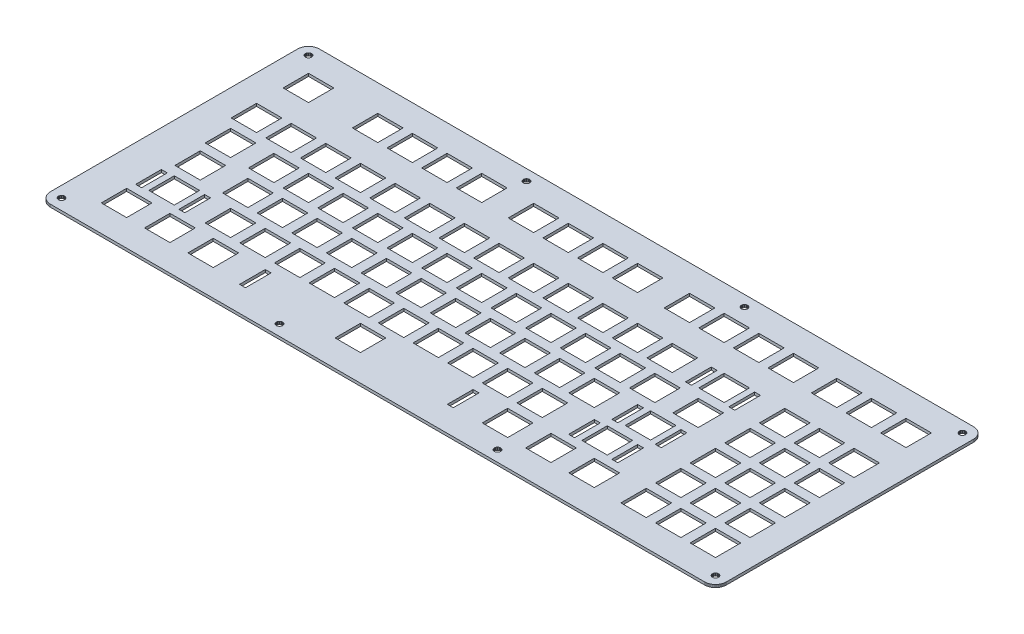
SolidWorks part; units mm, degrees
material "Copper"
ref_plane "Front Plane" through (0, 0, 0) normal (0, 0, 1) x (1, 0, 0)
ref_plane "Top Plane" through (0, 0, 0) normal (0, 1, 0) x (1, 0, 0)
ref_plane "Right Plane" through (0, 0, 0) normal (1, 0, 0) x (0, 0, -1)
sketch "Sketch2" plane through (0, 0, 0) normal (0, 1, 0) x (1, 0, 0)
  line L0 (365.806, 147.967) -> (366.279, 147.949)
  line L1 (366.279, 147.949) -> (366.748, 147.894)
  line L2 (366.748, 147.894) -> (367.21, 147.803)
  line L3 (367.21, 147.803) -> (367.661, 147.675)
  line L4 (367.661, 147.675) -> (368.106, 147.511)
  line L5 (368.106, 147.511) -> (368.533, 147.314)
  line L6 (368.533, 147.314) -> (368.942, 147.085)
  line L7 (368.942, 147.085) -> (369.334, 146.822)
  line L8 (369.334, 146.822) -> (369.704, 146.529)
  line L9 (369.704, 146.529) -> (370.05, 146.21)
  line L10 (370.05, 146.21) -> (370.371, 145.865)
  line L11 (370.371, 145.865) -> (370.664, 145.495)
  line L12 (370.664, 145.495) -> (370.925, 145.102)
  line L13 (370.925, 145.102) -> (371.154, 144.691)
  line L14 (371.154, 144.691) -> (371.352, 144.264)
  line L15 (371.352, 144.264) -> (371.514, 143.822)
  line L16 (371.514, 143.822) -> (371.641, 143.368)
  line L17 (371.641, 143.368) -> (371.733, 142.907)
  line L18 (371.733, 142.907) -> (371.789, 142.44)
  line L19 (371.789, 142.44) -> (371.807, 141.967)
  line L20 (371.807, 141.967) -> (371.807, 6.0909)
  line L21 (371.807, 6.0909) -> (371.789, 5.621)
  line L22 (371.789, 5.621) -> (371.733, 5.1539)
  line L23 (371.733, 5.1539) -> (371.641, 4.6909)
  line L24 (371.641, 4.6909) -> (371.514, 4.2375)
  line L25 (371.514, 4.2375) -> (371.352, 3.7951)
  line L26 (371.352, 3.7951) -> (371.154, 3.3679)
  line L27 (371.154, 3.3679) -> (370.925, 2.9573)
  line L28 (370.925, 2.9573) -> (370.664, 2.5645)
  line L29 (370.664, 2.5645) -> (370.371, 2.1966)
  line L30 (370.371, 2.1966) -> (370.05, 1.8493)
  line L31 (370.05, 1.8493) -> (369.704, 1.5296)
  line L32 (369.704, 1.5296) -> (369.334, 1.2375)
  line L33 (369.334, 1.2375) -> (368.942, 0.9757)
  line L34 (368.942, 0.9757) -> (368.533, 0.7455)
  line L35 (368.533, 0.7455) -> (368.106, 0.5498)
  line L36 (368.106, 0.5498) -> (367.661, 0.3859)
  line L37 (367.661, 0.3859) -> (367.21, 0.2577)
  line L38 (367.21, 0.2577) -> (366.748, 0.1654)
  line L39 (366.748, 0.1654) -> (366.279, 0.1102)
  line L40 (366.279, 0.1102) -> (365.806, 0.091)
  line L41 (365.806, 0.091) -> (6.095, 0.091)
  line L42 (6.095, 0.091) -> (5.6238, 0.1102)
  line L43 (5.6238, 0.1102) -> (5.1553, 0.1654)
  line L44 (5.1553, 0.1654) -> (4.6936, 0.2577)
  line L45 (4.6936, 0.2577) -> (4.2402, 0.3859)
  line L46 (4.2402, 0.3859) -> (3.7979, 0.5498)
  line L47 (3.7979, 0.5498) -> (3.3707, 0.7455)
  line L48 (3.3707, 0.7455) -> (2.96, 0.9757)
  line L49 (2.96, 0.9757) -> (2.5673, 1.2375)
  line L50 (2.5673, 1.2375) -> (2.198, 1.5296)
  line L51 (2.198, 1.5296) -> (1.8521, 1.8493)
  line L52 (1.8521, 1.8493) -> (1.5324, 2.1966)
  line L53 (1.5324, 2.1966) -> (1.2402, 2.5645)
  line L54 (1.2402, 2.5645) -> (0.9784, 2.9573)
  line L55 (0.9784, 2.9573) -> (0.7483, 3.3679)
  line L56 (0.7483, 3.3679) -> (0.5512, 3.7951)
  line L57 (0.5512, 3.7951) -> (0.3872, 4.2375)
  line L58 (0.3872, 4.2375) -> (0.2591, 4.6909)
  line L59 (0.2591, 4.6909) -> (0.1681, 5.1539)
  line L60 (0.1681, 5.1539) -> (0.113, 5.621)
  line L61 (0.113, 5.621) -> (0.0937, 6.0923)
  line L62 (0.0937, 6.0923) -> (0.0951, 141.967)
  line L63 (0.0951, 141.967) -> (0.113, 142.44)
  line L64 (0.113, 142.44) -> (0.1681, 142.907)
  line L65 (0.1681, 142.907) -> (0.2591, 143.368)
  line L66 (0.2591, 143.368) -> (0.3872, 143.822)
  line L67 (0.3872, 143.822) -> (0.5512, 144.264)
  line L68 (0.5512, 144.264) -> (0.7483, 144.691)
  line L69 (0.7483, 144.691) -> (0.9784, 145.102)
  line L70 (0.9784, 145.102) -> (1.2402, 145.495)
  line L71 (1.2402, 145.495) -> (1.5324, 145.865)
  line L72 (1.5324, 145.865) -> (1.8521, 146.21)
  line L73 (1.8521, 146.21) -> (2.198, 146.529)
  line L74 (2.198, 146.529) -> (2.5673, 146.822)
  line L75 (2.5673, 146.822) -> (2.96, 147.085)
  line L76 (2.96, 147.085) -> (3.3707, 147.314)
  line L77 (3.3707, 147.314) -> (3.7979, 147.511)
  line L78 (3.7979, 147.511) -> (4.2402, 147.675)
  line L79 (4.2402, 147.675) -> (4.6936, 147.803)
  line L80 (4.6936, 147.803) -> (5.1553, 147.894)
  line L81 (5.1553, 147.894) -> (5.6238, 147.949)
  line L82 (5.6238, 147.949) -> (6.095, 147.968)
  line L83 (6.095, 147.968) -> (365.806, 147.967)
  line L84 (365.252, 7.757) -> (364.769, 7.5117)
  line L85 (364.769, 7.5117) -> (364.388, 7.13)
  line L86 (364.388, 7.13) -> (364.141, 6.6504)
  line L87 (364.141, 6.6504) -> (364.06, 6.1157)
  line L88 (364.06, 6.1157) -> (364.141, 5.5838)
  line L89 (364.141, 5.5838) -> (364.388, 5.1029)
  line L90 (364.388, 5.1029) -> (364.769, 4.7211)
  line L91 (364.769, 4.7211) -> (365.252, 4.4759)
  line L92 (365.252, 4.4759) -> (365.781, 4.3918)
  line L93 (365.781, 4.3918) -> (366.317, 4.4759)
  line L94 (366.317, 4.4759) -> (366.797, 4.7211)
  line L95 (366.797, 4.7211) -> (367.178, 5.1029)
  line L96 (367.178, 5.1029) -> (367.425, 5.5838)
  line L97 (367.425, 5.5838) -> (367.506, 6.1157)
  line L98 (367.506, 6.1157) -> (367.425, 6.6504)
  line L99 (367.425, 6.6504) -> (367.178, 7.13)
  line L100 (367.178, 7.13) -> (366.797, 7.5117)
  line L101 (366.797, 7.5117) -> (366.317, 7.757)
  line L102 (366.317, 7.757) -> (365.781, 7.8411)
  line L103 (365.781, 7.8411) -> (365.252, 7.757)
  line L104 (245.361, 7.757) -> (244.88, 7.5117)
  line L105 (244.88, 7.5117) -> (244.5, 7.13)
  line L106 (244.5, 7.13) -> (244.255, 6.6504)
  line L107 (244.255, 6.6504) -> (244.169, 6.1157)
  line L108 (244.169, 6.1157) -> (244.255, 5.5838)
  line L109 (244.255, 5.5838) -> (244.5, 5.1029)
  line L110 (244.5, 5.1029) -> (244.88, 4.7211)
  line L111 (244.88, 4.7211) -> (245.361, 4.4759)
  line L112 (245.361, 4.4759) -> (245.894, 4.3918)
  line L113 (245.894, 4.3918) -> (246.428, 4.4759)
  line L114 (246.428, 4.4759) -> (246.908, 4.7211)
  line L115 (246.908, 4.7211) -> (247.29, 5.1029)
  line L116 (247.29, 5.1029) -> (247.536, 5.5838)
  line L117 (247.536, 5.5838) -> (247.62, 6.1157)
  line L118 (247.62, 6.1157) -> (247.536, 6.6504)
  line L119 (247.536, 6.6504) -> (247.29, 7.13)
  line L120 (247.29, 7.13) -> (246.908, 7.5117)
  line L121 (246.908, 7.5117) -> (246.428, 7.757)
  line L122 (246.428, 7.757) -> (245.894, 7.8411)
  line L123 (245.894, 7.8411) -> (245.361, 7.757)
  line L124 (125.473, 7.757) -> (124.992, 7.5117)
  line L125 (124.992, 7.5117) -> (124.612, 7.13)
  line L126 (124.612, 7.13) -> (124.365, 6.6504)
  line L127 (124.365, 6.6504) -> (124.281, 6.1157)
  line L128 (124.281, 6.1157) -> (124.365, 5.5838)
  line L129 (124.365, 5.5838) -> (124.612, 5.1029)
  line L130 (124.612, 5.1029) -> (124.992, 4.7211)
  line L131 (124.992, 4.7211) -> (125.473, 4.4759)
  line L132 (125.473, 4.4759) -> (126.007, 4.3918)
  line L133 (126.007, 4.3918) -> (126.54, 4.4759)
  line L134 (126.54, 4.4759) -> (127.021, 4.7211)
  line L135 (127.021, 4.7211) -> (127.403, 5.1029)
  line L136 (127.403, 5.1029) -> (127.648, 5.5838)
  line L137 (127.648, 5.5838) -> (127.732, 6.1157)
  line L138 (127.732, 6.1157) -> (127.648, 6.6504)
  line L139 (127.648, 6.6504) -> (127.403, 7.13)
  line L140 (127.403, 7.13) -> (127.021, 7.5117)
  line L141 (127.021, 7.5117) -> (126.54, 7.757)
  line L142 (126.54, 7.757) -> (126.007, 7.8411)
  line L143 (126.007, 7.8411) -> (125.473, 7.757)
  line L144 (5.5852, 7.757) -> (5.1056, 7.5117)
  line L145 (5.1056, 7.5117) -> (4.7239, 7.13)
  line L146 (4.7239, 7.13) -> (4.4786, 6.6504)
  line L147 (4.4786, 6.6504) -> (4.3932, 6.1157)
  line L148 (4.3932, 6.1157) -> (4.4786, 5.5838)
  line L149 (4.4786, 5.5838) -> (4.7239, 5.1029)
  line L150 (4.7239, 5.1029) -> (5.1056, 4.7211)
  line L151 (5.1056, 4.7211) -> (5.5852, 4.4759)
  line L152 (5.5852, 4.4759) -> (6.1185, 4.3918)
  line L153 (6.1185, 4.3918) -> (6.6532, 4.4759)
  line L154 (6.6532, 4.4759) -> (7.1327, 4.7211)
  line L155 (7.1327, 4.7211) -> (7.5145, 5.1029)
  line L156 (7.5145, 5.1029) -> (7.7597, 5.5838)
  line L157 (7.7597, 5.5838) -> (7.8438, 6.1157)
  line L158 (7.8438, 6.1157) -> (7.7597, 6.6504)
  line L159 (7.7597, 6.6504) -> (7.5145, 7.13)
  line L160 (7.5145, 7.13) -> (7.1327, 7.5117)
  line L161 (7.1327, 7.5117) -> (6.6532, 7.757)
  line L162 (6.6532, 7.757) -> (6.1185, 7.8411)
  line L163 (6.1185, 7.8411) -> (5.5852, 7.757)
  line L164 (96.2201, 28.0679) -> (99.4696, 28.0679)
  line L165 (99.4696, 28.0679) -> (99.4696, 13.9182)
  line L166 (99.4696, 13.9182) -> (96.2201, 13.9182)
  line L167 (96.2201, 13.9182) -> (96.2201, 28.0679)
  line L168 (210.52, 28.0679) -> (213.77, 28.0679)
  line L169 (213.77, 28.0679) -> (213.77, 13.9182)
  line L170 (213.77, 13.9182) -> (210.52, 13.9182)
  line L171 (210.52, 13.9182) -> (210.52, 28.0679)
  line L172 (19.4317, 28.6177) -> (33.3816, 28.6177)
  line L173 (33.3816, 28.6177) -> (33.3816, 14.6678)
  line L174 (33.3816, 14.6678) -> (19.4317, 14.6678)
  line L175 (19.4317, 14.6678) -> (19.4317, 28.6177)
  line L176 (43.2442, 28.6177) -> (57.1941, 28.6177)
  line L177 (57.1941, 28.6177) -> (57.1941, 14.6678)
  line L178 (57.1941, 14.6678) -> (43.2442, 14.6678)
  line L179 (43.2442, 14.6678) -> (43.2442, 28.6177)
  line L180 (67.0567, 28.6177) -> (81.0066, 28.6177)
  line L181 (81.0066, 28.6177) -> (81.0066, 14.6678)
  line L182 (81.0066, 14.6678) -> (67.0567, 14.6678)
  line L183 (67.0567, 14.6678) -> (67.0567, 28.6177)
  line L184 (148.019, 28.6177) -> (161.969, 28.6177)
  line L185 (161.969, 28.6177) -> (161.969, 14.6678)
  line L186 (161.969, 14.6678) -> (148.019, 14.6678)
  line L187 (148.019, 14.6678) -> (148.019, 28.6177)
  line L188 (228.982, 28.6177) -> (242.932, 28.6177)
  line L189 (242.932, 28.6177) -> (242.932, 14.6678)
  line L190 (242.932, 14.6678) -> (228.982, 14.6678)
  line L191 (228.982, 14.6678) -> (228.982, 28.6177)
  line L192 (252.794, 28.6177) -> (266.744, 28.6177)
  line L193 (266.744, 28.6177) -> (266.744, 14.6678)
  line L194 (266.744, 14.6678) -> (252.794, 14.6678)
  line L195 (252.794, 14.6678) -> (252.794, 28.6177)
  line L196 (276.607, 28.6177) -> (290.557, 28.6177)
  line L197 (290.557, 28.6177) -> (290.557, 14.6678)
  line L198 (290.557, 14.6678) -> (276.607, 14.6678)
  line L199 (276.607, 14.6678) -> (276.607, 28.6177)
  line L200 (305.182, 28.6177) -> (319.132, 28.6177)
  line L201 (319.132, 28.6177) -> (319.132, 14.6678)
  line L202 (319.132, 14.6678) -> (305.182, 14.6678)
  line L203 (305.182, 14.6678) -> (305.182, 28.6177)
  line L204 (324.232, 28.6177) -> (338.182, 28.6177)
  line L205 (338.182, 28.6177) -> (338.182, 14.6678)
  line L206 (338.182, 14.6678) -> (324.232, 14.6678)
  line L207 (324.232, 14.6678) -> (324.232, 28.6177)
  line L208 (343.282, 28.6177) -> (357.233, 28.6177)
  line L209 (357.233, 28.6177) -> (357.233, 14.6678)
  line L210 (357.233, 14.6678) -> (343.282, 14.6678)
  line L211 (343.282, 14.6678) -> (343.282, 28.6177)
  line L212 (20.0256, 47.1166) -> (23.2751, 47.1166)
  line L213 (23.2751, 47.1166) -> (23.2751, 32.9682)
  line L214 (23.2751, 32.9682) -> (20.0256, 32.9682)
  line L215 (20.0256, 32.9682) -> (20.0256, 47.1166)
  line L216 (43.8256, 47.1166) -> (47.075, 47.1166)
  line L217 (47.075, 47.1166) -> (47.075, 32.9682)
  line L218 (47.075, 32.9682) -> (43.8256, 32.9682)
  line L219 (43.8256, 32.9682) -> (43.8256, 47.1166)
  line L220 (258.151, 47.1166) -> (261.4, 47.1166)
  line L221 (261.4, 47.1166) -> (261.4, 32.9682)
  line L222 (261.4, 32.9682) -> (258.151, 32.9682)
  line L223 (258.151, 32.9682) -> (258.151, 47.1166)
  line L224 (281.951, 47.1166) -> (285.2, 47.1166)
  line L225 (285.2, 47.1166) -> (285.2, 32.9682)
  line L226 (285.2, 32.9682) -> (281.951, 32.9682)
  line L227 (281.951, 32.9682) -> (281.951, 47.1166)
  line L228 (26.5755, 47.6677) -> (40.5253, 47.6677)
  line L229 (40.5253, 47.6677) -> (40.5253, 33.7178)
  line L230 (40.5253, 33.7178) -> (26.5755, 33.7178)
  line L231 (26.5755, 33.7178) -> (26.5755, 47.6677)
  line L232 (57.5317, 47.6677) -> (71.4816, 47.6677)
  line L233 (71.4816, 47.6677) -> (71.4816, 33.7178)
  line L234 (71.4816, 33.7178) -> (57.5317, 33.7178)
  line L235 (57.5317, 33.7178) -> (57.5317, 47.6677)
  line L236 (76.5817, 47.6677) -> (90.5316, 47.6677)
  line L237 (90.5316, 47.6677) -> (90.5316, 33.7178)
  line L238 (90.5316, 33.7178) -> (76.5817, 33.7178)
  line L239 (76.5817, 33.7178) -> (76.5817, 47.6677)
  line L240 (95.6317, 47.6677) -> (109.582, 47.6677)
  line L241 (109.582, 47.6677) -> (109.582, 33.7178)
  line L242 (109.582, 33.7178) -> (95.6317, 33.7178)
  line L243 (95.6317, 33.7178) -> (95.6317, 47.6677)
  line L244 (114.682, 47.6677) -> (128.632, 47.6677)
  line L245 (128.632, 47.6677) -> (128.632, 33.7178)
  line L246 (128.632, 33.7178) -> (114.682, 33.7178)
  line L247 (114.682, 33.7178) -> (114.682, 47.6677)
  line L248 (133.732, 47.6677) -> (147.682, 47.6677)
  line L249 (147.682, 47.6677) -> (147.682, 33.7178)
  line L250 (147.682, 33.7178) -> (133.732, 33.7178)
  line L251 (133.732, 33.7178) -> (133.732, 47.6677)
  line L252 (152.782, 47.6677) -> (166.732, 47.6677)
  line L253 (166.732, 47.6677) -> (166.732, 33.7178)
  line L254 (166.732, 33.7178) -> (152.782, 33.7178)
  line L255 (152.782, 33.7178) -> (152.782, 47.6677)
  line L256 (171.832, 47.6677) -> (185.782, 47.6677)
  line L257 (185.782, 47.6677) -> (185.782, 33.7178)
  line L258 (185.782, 33.7178) -> (171.832, 33.7178)
  line L259 (171.832, 33.7178) -> (171.832, 47.6677)
  line L260 (190.882, 47.6677) -> (204.832, 47.6677)
  line L261 (204.832, 47.6677) -> (204.832, 33.7178)
  line L262 (204.832, 33.7178) -> (190.882, 33.7178)
  line L263 (190.882, 33.7178) -> (190.882, 47.6677)
  line L264 (209.932, 47.6677) -> (223.882, 47.6677)
  line L265 (223.882, 47.6677) -> (223.882, 33.7178)
  line L266 (223.882, 33.7178) -> (209.932, 33.7178)
  line L267 (209.932, 33.7178) -> (209.932, 47.6677)
  line L268 (228.982, 47.6677) -> (242.932, 47.6677)
  line L269 (242.932, 47.6677) -> (242.932, 33.7178)
  line L270 (242.932, 33.7178) -> (228.982, 33.7178)
  line L271 (228.982, 33.7178) -> (228.982, 47.6677)
  line L272 (264.7, 47.6677) -> (278.65, 47.6677)
  line L273 (278.65, 47.6677) -> (278.65, 33.7178)
  line L274 (278.65, 33.7178) -> (264.7, 33.7178)
  line L275 (264.7, 33.7178) -> (264.7, 47.6677)
  line L276 (305.182, 47.6677) -> (319.132, 47.6677)
  line L277 (319.132, 47.6677) -> (319.132, 33.7178)
  line L278 (319.132, 33.7178) -> (305.182, 33.7178)
  line L279 (305.182, 33.7178) -> (305.182, 47.6677)
  line L280 (324.232, 47.6677) -> (338.182, 47.6677)
  line L281 (338.182, 47.6677) -> (338.182, 33.7178)
  line L282 (338.182, 33.7178) -> (324.232, 33.7178)
  line L283 (324.232, 33.7178) -> (324.232, 47.6677)
  line L284 (343.282, 47.6677) -> (357.233, 47.6677)
  line L285 (357.233, 47.6677) -> (357.233, 33.7178)
  line L286 (357.233, 33.7178) -> (343.282, 33.7178)
  line L287 (343.282, 33.7178) -> (343.282, 47.6677)
  line L288 (262.913, 66.1666) -> (266.163, 66.1666)
  line L289 (266.163, 66.1666) -> (266.163, 52.0181)
  line L290 (266.163, 52.0181) -> (262.913, 52.0181)
  line L291 (262.913, 52.0181) -> (262.913, 66.1666)
  line L292 (286.713, 66.1666) -> (289.963, 66.1666)
  line L293 (289.963, 66.1666) -> (289.963, 52.0181)
  line L294 (289.963, 52.0181) -> (286.713, 52.0181)
  line L295 (286.713, 52.0181) -> (286.713, 66.1666)
  line L296 (21.813, 66.7177) -> (35.7628, 66.7177)
  line L297 (35.7628, 66.7177) -> (35.7628, 52.7678)
  line L298 (35.7628, 52.7678) -> (21.813, 52.7678)
  line L299 (21.813, 52.7678) -> (21.813, 66.7177)
  line L300 (48.0067, 66.7177) -> (61.9566, 66.7177)
  line L301 (61.9566, 66.7177) -> (61.9566, 52.7678)
  line L302 (61.9566, 52.7678) -> (48.0067, 52.7678)
  line L303 (48.0067, 52.7678) -> (48.0067, 66.7177)
  line L304 (67.0567, 66.7177) -> (81.0066, 66.7177)
  line L305 (81.0066, 66.7177) -> (81.0066, 52.7678)
  line L306 (81.0066, 52.7678) -> (67.0567, 52.7678)
  line L307 (67.0567, 52.7678) -> (67.0567, 66.7177)
  line L308 (86.1067, 66.7177) -> (100.057, 66.7177)
  line L309 (100.057, 66.7177) -> (100.057, 52.7678)
  line L310 (100.057, 52.7678) -> (86.1067, 52.7678)
  line L311 (86.1067, 52.7678) -> (86.1067, 66.7177)
  line L312 (105.157, 66.7177) -> (119.107, 66.7177)
  line L313 (119.107, 66.7177) -> (119.107, 52.7678)
  line L314 (119.107, 52.7678) -> (105.157, 52.7678)
  line L315 (105.157, 52.7678) -> (105.157, 66.7177)
  line L316 (124.207, 66.7177) -> (138.157, 66.7177)
  line L317 (138.157, 66.7177) -> (138.157, 52.7678)
  line L318 (138.157, 52.7678) -> (124.207, 52.7678)
  line L319 (124.207, 52.7678) -> (124.207, 66.7177)
  line L320 (143.257, 66.7177) -> (157.207, 66.7177)
  line L321 (157.207, 66.7177) -> (157.207, 52.7678)
  line L322 (157.207, 52.7678) -> (143.257, 52.7678)
  line L323 (143.257, 52.7678) -> (143.257, 66.7177)
  line L324 (162.307, 66.7177) -> (176.257, 66.7177)
  line L325 (176.257, 66.7177) -> (176.257, 52.7678)
  line L326 (176.257, 52.7678) -> (162.307, 52.7678)
  line L327 (162.307, 52.7678) -> (162.307, 66.7177)
  line L328 (181.357, 66.7177) -> (195.307, 66.7177)
  line L329 (195.307, 66.7177) -> (195.307, 52.7678)
  line L330 (195.307, 52.7678) -> (181.357, 52.7678)
  line L331 (181.357, 52.7678) -> (181.357, 66.7177)
  line L332 (200.407, 66.7177) -> (214.357, 66.7177)
  line L333 (214.357, 66.7177) -> (214.357, 52.7678)
  line L334 (214.357, 52.7678) -> (200.407, 52.7678)
  line L335 (200.407, 52.7678) -> (200.407, 66.7177)
  line L336 (219.457, 66.7177) -> (233.407, 66.7177)
  line L337 (233.407, 66.7177) -> (233.407, 52.7678)
  line L338 (233.407, 52.7678) -> (219.457, 52.7678)
  line L339 (219.457, 52.7678) -> (219.457, 66.7177)
  line L340 (238.507, 66.7177) -> (252.457, 66.7177)
  line L341 (252.457, 66.7177) -> (252.457, 52.7678)
  line L342 (252.457, 52.7678) -> (238.507, 52.7678)
  line L343 (238.507, 52.7678) -> (238.507, 66.7177)
  line L344 (269.463, 66.7177) -> (283.413, 66.7177)
  line L345 (283.413, 66.7177) -> (283.413, 52.7678)
  line L346 (283.413, 52.7678) -> (269.463, 52.7678)
  line L347 (269.463, 52.7678) -> (269.463, 66.7177)
  line L348 (305.182, 66.7177) -> (319.132, 66.7177)
  line L349 (319.132, 66.7177) -> (319.132, 52.7678)
  line L350 (319.132, 52.7678) -> (305.182, 52.7678)
  line L351 (305.182, 52.7678) -> (305.182, 66.7177)
  line L352 (324.232, 66.7177) -> (338.182, 66.7177)
  line L353 (338.182, 66.7177) -> (338.182, 52.7678)
  line L354 (338.182, 52.7678) -> (324.232, 52.7678)
  line L355 (324.232, 52.7678) -> (324.232, 66.7177)
  line L356 (343.282, 66.7177) -> (357.233, 66.7177)
  line L357 (357.233, 66.7177) -> (357.233, 52.7678)
  line L358 (357.233, 52.7678) -> (343.282, 52.7678)
  line L359 (343.282, 52.7678) -> (343.282, 66.7177)
  line L360 (19.4317, 85.7677) -> (33.3816, 85.7677)
  line L361 (33.3816, 85.7677) -> (33.3816, 71.8178)
  line L362 (33.3816, 71.8178) -> (19.4317, 71.8178)
  line L363 (19.4317, 71.8178) -> (19.4317, 85.7677)
  line L364 (43.2442, 85.7677) -> (57.1941, 85.7677)
  line L365 (57.1941, 85.7677) -> (57.1941, 71.8178)
  line L366 (57.1941, 71.8178) -> (43.2442, 71.8178)
  line L367 (43.2442, 71.8178) -> (43.2442, 85.7677)
  line L368 (62.2942, 85.7677) -> (76.2441, 85.7677)
  line L369 (76.2441, 85.7677) -> (76.2441, 71.8178)
  line L370 (76.2441, 71.8178) -> (62.2942, 71.8178)
  line L371 (62.2942, 71.8178) -> (62.2942, 85.7677)
  line L372 (81.3442, 85.7677) -> (95.2941, 85.7677)
  line L373 (95.2941, 85.7677) -> (95.2941, 71.8178)
  line L374 (95.2941, 71.8178) -> (81.3442, 71.8178)
  line L375 (81.3442, 71.8178) -> (81.3442, 85.7677)
  line L376 (100.394, 85.7677) -> (114.344, 85.7677)
  line L377 (114.344, 85.7677) -> (114.344, 71.8178)
  line L378 (114.344, 71.8178) -> (100.394, 71.8178)
  line L379 (100.394, 71.8178) -> (100.394, 85.7677)
  line L380 (119.444, 85.7677) -> (133.394, 85.7677)
  line L381 (133.394, 85.7677) -> (133.394, 71.8178)
  line L382 (133.394, 71.8178) -> (119.444, 71.8178)
  line L383 (119.444, 71.8178) -> (119.444, 85.7677)
  line L384 (138.494, 85.7677) -> (152.444, 85.7677)
  line L385 (152.444, 85.7677) -> (152.444, 71.8178)
  line L386 (152.444, 71.8178) -> (138.494, 71.8178)
  line L387 (138.494, 71.8178) -> (138.494, 85.7677)
  line L388 (157.544, 85.7677) -> (171.494, 85.7677)
  line L389 (171.494, 85.7677) -> (171.494, 71.8178)
  line L390 (171.494, 71.8178) -> (157.544, 71.8178)
  line L391 (157.544, 71.8178) -> (157.544, 85.7677)
  line L392 (176.594, 85.7677) -> (190.544, 85.7677)
  line L393 (190.544, 85.7677) -> (190.544, 71.8178)
  line L394 (190.544, 71.8178) -> (176.594, 71.8178)
  line L395 (176.594, 71.8178) -> (176.594, 85.7677)
  line L396 (195.644, 85.7677) -> (209.594, 85.7677)
  line L397 (209.594, 85.7677) -> (209.594, 71.8178)
  line L398 (209.594, 71.8178) -> (195.644, 71.8178)
  line L399 (195.644, 71.8178) -> (195.644, 85.7677)
  line L400 (214.694, 85.7677) -> (228.644, 85.7677)
  line L401 (228.644, 85.7677) -> (228.644, 71.8178)
  line L402 (228.644, 71.8178) -> (214.694, 71.8178)
  line L403 (214.694, 71.8178) -> (214.694, 85.7677)
  line L404 (233.744, 85.7677) -> (247.694, 85.7677)
  line L405 (247.694, 85.7677) -> (247.694, 71.8178)
  line L406 (247.694, 71.8178) -> (233.744, 71.8178)
  line L407 (233.744, 71.8178) -> (233.744, 85.7677)
  line L408 (252.794, 85.7677) -> (266.744, 85.7677)
  line L409 (266.744, 85.7677) -> (266.744, 71.8178)
  line L410 (266.744, 71.8178) -> (252.794, 71.8178)
  line L411 (252.794, 71.8178) -> (252.794, 85.7677)
  line L412 (276.607, 85.7677) -> (290.557, 85.7677)
  line L413 (290.557, 85.7677) -> (290.557, 71.8178)
  line L414 (290.557, 71.8178) -> (276.607, 71.8178)
  line L415 (276.607, 71.8178) -> (276.607, 85.7677)
  line L416 (305.182, 85.7677) -> (319.132, 85.7677)
  line L417 (319.132, 85.7677) -> (319.132, 71.8178)
  line L418 (319.132, 71.8178) -> (305.182, 71.8178)
  line L419 (305.182, 71.8178) -> (305.182, 85.7677)
  line L420 (324.232, 85.7677) -> (338.182, 85.7677)
  line L421 (338.182, 85.7677) -> (338.182, 71.8178)
  line L422 (338.182, 71.8178) -> (324.232, 71.8178)
  line L423 (324.232, 71.8178) -> (324.232, 85.7677)
  line L424 (343.282, 85.7677) -> (357.233, 85.7677)
  line L425 (357.233, 85.7677) -> (357.233, 71.8178)
  line L426 (357.233, 71.8178) -> (343.282, 71.8178)
  line L427 (343.282, 71.8178) -> (343.282, 85.7677)
  line L428 (265.295, 104.267) -> (268.545, 104.267)
  line L429 (268.545, 104.267) -> (268.545, 90.1167)
  line L430 (268.545, 90.1167) -> (265.295, 90.1167)
  line L431 (265.295, 90.1167) -> (265.295, 104.267)
  line L432 (289.094, 104.267) -> (292.345, 104.267)
  line L433 (292.345, 104.267) -> (292.345, 90.1167)
  line L434 (292.345, 90.1167) -> (289.094, 90.1167)
  line L435 (289.094, 90.1167) -> (289.094, 104.267)
  line L436 (14.6692, 104.818) -> (28.6191, 104.818)
  line L437 (28.6191, 104.818) -> (28.6191, 90.8678)
  line L438 (28.6191, 90.8678) -> (14.6692, 90.8678)
  line L439 (14.6692, 90.8678) -> (14.6692, 104.818)
  line L440 (33.7192, 104.818) -> (47.6691, 104.818)
  line L441 (47.6691, 104.818) -> (47.6691, 90.8678)
  line L442 (47.6691, 90.8678) -> (33.7192, 90.8678)
  line L443 (33.7192, 90.8678) -> (33.7192, 104.818)
  line L444 (52.7692, 104.818) -> (66.7191, 104.818)
  line L445 (66.7191, 104.818) -> (66.7191, 90.8678)
  line L446 (66.7191, 90.8678) -> (52.7692, 90.8678)
  line L447 (52.7692, 90.8678) -> (52.7692, 104.818)
  line L448 (71.8192, 104.818) -> (85.7691, 104.818)
  line L449 (85.7691, 104.818) -> (85.7691, 90.8678)
  line L450 (85.7691, 90.8678) -> (71.8192, 90.8678)
  line L451 (71.8192, 90.8678) -> (71.8192, 104.818)
  line L452 (90.8692, 104.818) -> (104.819, 104.818)
  line L453 (104.819, 104.818) -> (104.819, 90.8678)
  line L454 (104.819, 90.8678) -> (90.8692, 90.8678)
  line L455 (90.8692, 90.8678) -> (90.8692, 104.818)
  line L456 (109.919, 104.818) -> (123.869, 104.818)
  line L457 (123.869, 104.818) -> (123.869, 90.8678)
  line L458 (123.869, 90.8678) -> (109.919, 90.8678)
  line L459 (109.919, 90.8678) -> (109.919, 104.818)
  line L460 (128.969, 104.818) -> (142.919, 104.818)
  line L461 (142.919, 104.818) -> (142.919, 90.8678)
  line L462 (142.919, 90.8678) -> (128.969, 90.8678)
  line L463 (128.969, 90.8678) -> (128.969, 104.818)
  line L464 (148.019, 104.818) -> (161.969, 104.818)
  line L465 (161.969, 104.818) -> (161.969, 90.8678)
  line L466 (161.969, 90.8678) -> (148.019, 90.8678)
  line L467 (148.019, 90.8678) -> (148.019, 104.818)
  line L468 (167.069, 104.818) -> (181.019, 104.818)
  line L469 (181.019, 104.818) -> (181.019, 90.8678)
  line L470 (181.019, 90.8678) -> (167.069, 90.8678)
  line L471 (167.069, 90.8678) -> (167.069, 104.818)
  line L472 (186.119, 104.818) -> (200.069, 104.818)
  line L473 (200.069, 104.818) -> (200.069, 90.8678)
  line L474 (200.069, 90.8678) -> (186.119, 90.8678)
  line L475 (186.119, 90.8678) -> (186.119, 104.818)
  line L476 (205.169, 104.818) -> (219.119, 104.818)
  line L477 (219.119, 104.818) -> (219.119, 90.8678)
  line L478 (219.119, 90.8678) -> (205.169, 90.8678)
  line L479 (205.169, 90.8678) -> (205.169, 104.818)
  line L480 (224.219, 104.818) -> (238.169, 104.818)
  line L481 (238.169, 104.818) -> (238.169, 90.8678)
  line L482 (238.169, 90.8678) -> (224.219, 90.8678)
  line L483 (224.219, 90.8678) -> (224.219, 104.818)
  line L484 (243.269, 104.818) -> (257.219, 104.818)
  line L485 (257.219, 104.818) -> (257.219, 90.8678)
  line L486 (257.219, 90.8678) -> (243.269, 90.8678)
  line L487 (243.269, 90.8678) -> (243.269, 104.818)
  line L488 (271.844, 104.818) -> (285.794, 104.818)
  line L489 (285.794, 104.818) -> (285.794, 90.8678)
  line L490 (285.794, 90.8678) -> (271.844, 90.8678)
  line L491 (271.844, 90.8678) -> (271.844, 104.818)
  line L492 (305.182, 104.818) -> (319.132, 104.818)
  line L493 (319.132, 104.818) -> (319.132, 90.8678)
  line L494 (319.132, 90.8678) -> (305.182, 90.8678)
  line L495 (305.182, 90.8678) -> (305.182, 104.818)
  line L496 (324.232, 104.818) -> (338.182, 104.818)
  line L497 (338.182, 104.818) -> (338.182, 90.8678)
  line L498 (338.182, 90.8678) -> (324.232, 90.8678)
  line L499 (324.232, 90.8678) -> (324.232, 104.818)
  line L500 (343.282, 104.818) -> (357.233, 104.818)
  line L501 (357.233, 104.818) -> (357.233, 90.8678)
  line L502 (357.233, 90.8678) -> (343.282, 90.8678)
  line L503 (343.282, 90.8678) -> (343.282, 104.818)
  line L504 (14.6692, 133.393) -> (28.6191, 133.393)
  line L505 (28.6191, 133.393) -> (28.6191, 119.443)
  line L506 (28.6191, 119.443) -> (14.6692, 119.443)
  line L507 (14.6692, 119.443) -> (14.6692, 133.393)
  line L508 (52.7692, 133.393) -> (66.7191, 133.393)
  line L509 (66.7191, 133.393) -> (66.7191, 119.443)
  line L510 (66.7191, 119.443) -> (52.7692, 119.443)
  line L511 (52.7692, 119.443) -> (52.7692, 133.393)
  line L512 (71.8192, 133.393) -> (85.7691, 133.393)
  line L513 (85.7691, 133.393) -> (85.7691, 119.443)
  line L514 (85.7691, 119.443) -> (71.8192, 119.443)
  line L515 (71.8192, 119.443) -> (71.8192, 133.393)
  line L516 (90.8692, 133.393) -> (104.819, 133.393)
  line L517 (104.819, 133.393) -> (104.819, 119.443)
  line L518 (104.819, 119.443) -> (90.8692, 119.443)
  line L519 (90.8692, 119.443) -> (90.8692, 133.393)
  line L520 (109.919, 133.393) -> (123.869, 133.393)
  line L521 (123.869, 133.393) -> (123.869, 119.443)
  line L522 (123.869, 119.443) -> (109.919, 119.443)
  line L523 (109.919, 119.443) -> (109.919, 133.393)
  line L524 (138.494, 133.393) -> (152.444, 133.393)
  line L525 (152.444, 133.393) -> (152.444, 119.443)
  line L526 (152.444, 119.443) -> (138.494, 119.443)
  line L527 (138.494, 119.443) -> (138.494, 133.393)
  line L528 (157.544, 133.393) -> (171.494, 133.393)
  line L529 (171.494, 133.393) -> (171.494, 119.443)
  line L530 (171.494, 119.443) -> (157.544, 119.443)
  line L531 (157.544, 119.443) -> (157.544, 133.393)
  line L532 (176.594, 133.393) -> (190.544, 133.393)
  line L533 (190.544, 133.393) -> (190.544, 119.443)
  line L534 (190.544, 119.443) -> (176.594, 119.443)
  line L535 (176.594, 119.443) -> (176.594, 133.393)
  line L536 (195.644, 133.393) -> (209.594, 133.393)
  line L537 (209.594, 133.393) -> (209.594, 119.443)
  line L538 (209.594, 119.443) -> (195.644, 119.443)
  line L539 (195.644, 119.443) -> (195.644, 133.393)
  line L540 (224.219, 133.393) -> (238.169, 133.393)
  line L541 (238.169, 133.393) -> (238.169, 119.443)
  line L542 (238.169, 119.443) -> (224.219, 119.443)
  line L543 (224.219, 119.443) -> (224.219, 133.393)
  line L544 (243.269, 133.393) -> (257.219, 133.393)
  line L545 (257.219, 133.393) -> (257.219, 119.443)
  line L546 (257.219, 119.443) -> (243.269, 119.443)
  line L547 (243.269, 119.443) -> (243.269, 133.393)
  line L548 (262.319, 133.393) -> (276.269, 133.393)
  line L549 (276.269, 133.393) -> (276.269, 119.443)
  line L550 (276.269, 119.443) -> (262.319, 119.443)
  line L551 (262.319, 119.443) -> (262.319, 133.393)
  line L552 (281.369, 133.393) -> (295.319, 133.393)
  line L553 (295.319, 133.393) -> (295.319, 119.443)
  line L554 (295.319, 119.443) -> (281.369, 119.443)
  line L555 (281.369, 119.443) -> (281.369, 133.393)
  line L556 (305.182, 133.393) -> (319.132, 133.393)
  line L557 (319.132, 133.393) -> (319.132, 119.443)
  line L558 (319.132, 119.443) -> (305.182, 119.443)
  line L559 (305.182, 119.443) -> (305.182, 133.393)
  line L560 (324.232, 133.393) -> (338.182, 133.393)
  line L561 (338.182, 133.393) -> (338.182, 119.443)
  line L562 (338.182, 119.443) -> (324.232, 119.443)
  line L563 (324.232, 119.443) -> (324.232, 133.393)
  line L564 (343.282, 133.393) -> (357.233, 133.393)
  line L565 (357.233, 133.393) -> (357.233, 119.443)
  line L566 (357.233, 119.443) -> (343.282, 119.443)
  line L567 (343.282, 119.443) -> (343.282, 133.393)
  line L568 (125.473, 143.583) -> (124.992, 143.338)
  line L569 (124.992, 143.338) -> (124.612, 142.956)
  line L570 (124.612, 142.956) -> (124.365, 142.477)
  line L571 (124.365, 142.477) -> (124.281, 141.942)
  line L572 (124.281, 141.942) -> (124.365, 141.409)
  line L573 (124.365, 141.409) -> (124.612, 140.929)
  line L574 (124.612, 140.929) -> (124.992, 140.547)
  line L575 (124.992, 140.547) -> (125.473, 140.302)
  line L576 (125.473, 140.302) -> (126.007, 140.217)
  line L577 (126.007, 140.217) -> (126.54, 140.302)
  line L578 (126.54, 140.302) -> (127.021, 140.547)
  line L579 (127.021, 140.547) -> (127.403, 140.929)
  line L580 (127.403, 140.929) -> (127.648, 141.409)
  line L581 (127.648, 141.409) -> (127.732, 141.942)
  line L582 (127.732, 141.942) -> (127.648, 142.477)
  line L583 (127.648, 142.477) -> (127.403, 142.956)
  line L584 (127.403, 142.956) -> (127.021, 143.338)
  line L585 (127.021, 143.338) -> (126.54, 143.583)
  line L586 (126.54, 143.583) -> (126.007, 143.667)
  line L587 (126.007, 143.667) -> (125.473, 143.583)
  line L588 (245.361, 143.583) -> (244.88, 143.338)
  line L589 (244.88, 143.338) -> (244.5, 142.956)
  line L590 (244.5, 142.956) -> (244.255, 142.477)
  line L591 (244.255, 142.477) -> (244.169, 141.942)
  line L592 (244.169, 141.942) -> (244.255, 141.409)
  line L593 (244.255, 141.409) -> (244.5, 140.929)
  line L594 (244.5, 140.929) -> (244.88, 140.547)
  line L595 (244.88, 140.547) -> (245.361, 140.302)
  line L596 (245.361, 140.302) -> (245.894, 140.217)
  line L597 (245.894, 140.217) -> (246.428, 140.302)
  line L598 (246.428, 140.302) -> (246.908, 140.547)
  line L599 (246.908, 140.547) -> (247.29, 140.929)
  line L600 (247.29, 140.929) -> (247.536, 141.409)
  line L601 (247.536, 141.409) -> (247.62, 141.942)
  line L602 (247.62, 141.942) -> (247.536, 142.477)
  line L603 (247.536, 142.477) -> (247.29, 142.956)
  line L604 (247.29, 142.956) -> (246.908, 143.338)
  line L605 (246.908, 143.338) -> (246.428, 143.583)
  line L606 (246.428, 143.583) -> (245.894, 143.667)
  line L607 (245.894, 143.667) -> (245.361, 143.583)
  line L608 (365.252, 143.583) -> (364.769, 143.338)
  line L609 (364.769, 143.338) -> (364.388, 142.956)
  line L610 (364.388, 142.956) -> (364.141, 142.477)
  line L611 (364.141, 142.477) -> (364.06, 141.942)
  line L612 (364.06, 141.942) -> (364.141, 141.409)
  line L613 (364.141, 141.409) -> (364.388, 140.929)
  line L614 (364.388, 140.929) -> (364.769, 140.547)
  line L615 (364.769, 140.547) -> (365.252, 140.302)
  line L616 (365.252, 140.302) -> (365.781, 140.217)
  line L617 (365.781, 140.217) -> (366.317, 140.302)
  line L618 (366.317, 140.302) -> (366.797, 140.547)
  line L619 (366.797, 140.547) -> (367.178, 140.929)
  line L620 (367.178, 140.929) -> (367.425, 141.409)
  line L621 (367.425, 141.409) -> (367.506, 141.942)
  line L622 (367.506, 141.942) -> (367.425, 142.477)
  line L623 (367.425, 142.477) -> (367.178, 142.956)
  line L624 (367.178, 142.956) -> (366.797, 143.338)
  line L625 (366.797, 143.338) -> (366.317, 143.583)
  line L626 (366.317, 143.583) -> (365.781, 143.667)
  line L627 (365.781, 143.667) -> (365.252, 143.583)
  line L628 (5.5852, 143.583) -> (5.1056, 143.338)
  line L629 (5.1056, 143.338) -> (4.7239, 142.956)
  line L630 (4.7239, 142.956) -> (4.4786, 142.477)
  line L631 (4.4786, 142.477) -> (4.3932, 141.942)
  line L632 (4.3932, 141.942) -> (4.4786, 141.409)
  line L633 (4.4786, 141.409) -> (4.7239, 140.929)
  line L634 (4.7239, 140.929) -> (5.1056, 140.547)
  line L635 (5.1056, 140.547) -> (5.5852, 140.302)
  line L636 (5.5852, 140.302) -> (6.1185, 140.217)
  line L637 (6.1185, 140.217) -> (6.6532, 140.302)
  line L638 (6.6532, 140.302) -> (7.1327, 140.547)
  line L639 (7.1327, 140.547) -> (7.5145, 140.929)
  line L640 (7.5145, 140.929) -> (7.7597, 141.409)
  line L641 (7.7597, 141.409) -> (7.8438, 141.942)
  line L642 (7.8438, 141.942) -> (7.7597, 142.477)
  line L643 (7.7597, 142.477) -> (7.5145, 142.956)
  line L644 (7.5145, 142.956) -> (7.1327, 143.338)
  line L645 (7.1327, 143.338) -> (6.6532, 143.583)
  line L646 (6.6532, 143.583) -> (6.1185, 143.667)
  line L647 (6.1185, 143.667) -> (5.5852, 143.583)
extrude "Boss-Extrude1" add sketch "Sketch2" along normal blind 1.5
